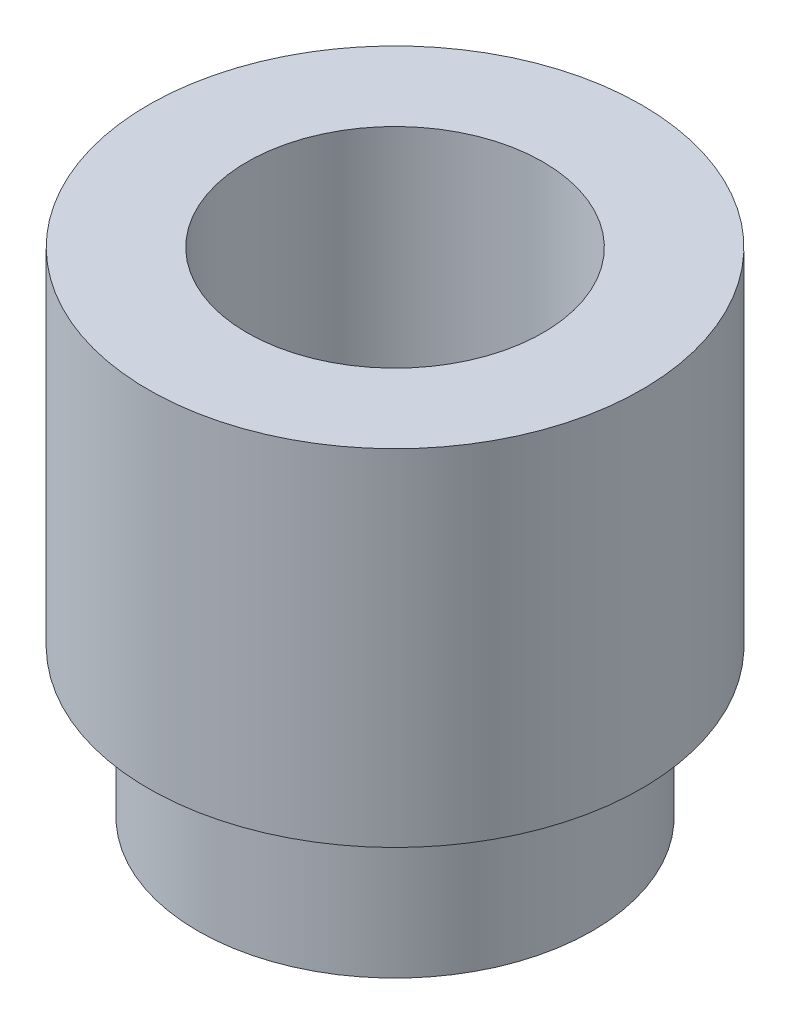
SolidWorks part; units mm, degrees
material "Brass"
ref_plane "Front Plane" through (0, 0, 0) normal (0, 0, 1) x (1, 0, 0)
ref_plane "Top Plane" through (0, 0, 0) normal (0, 1, 0) x (1, 0, 0)
ref_plane "Right Plane" through (0, 0, 0) normal (1, 0, 0) x (0, 0, -1)
sketch "Sketch1" plane through (0, 0, 0) normal (1, 0, 0) x (0, 0, -1)
  line L0 (1.5, 0) -> (1.5, 5)
  line L1 (1.5, 5) -> (2.5, 5)
  line L2 (2.5, 5) -> (2.5, 1.5)
  line L3 (2.5, 1.5) -> (2, 1.5)
  line L4 (2, 1.5) -> (2, 0)
  line L5 (2, 0) -> (1.5, 0)
  line L6 (0, 0) -> (0, 5) construction
  line L7 (0, 5) -> (1.5, 5) construction
  point P10 (0, 0)
  point P11 (1.75, 1.6025)
  dimension "D1" = 3
  dimension "D2" = 5
  dimension "D3" = 4
  dimension "D4" = 5
  dimension "D5" = 1.5
revolve "Revolve1" add sketch "Sketch1" angle 360 about L6
